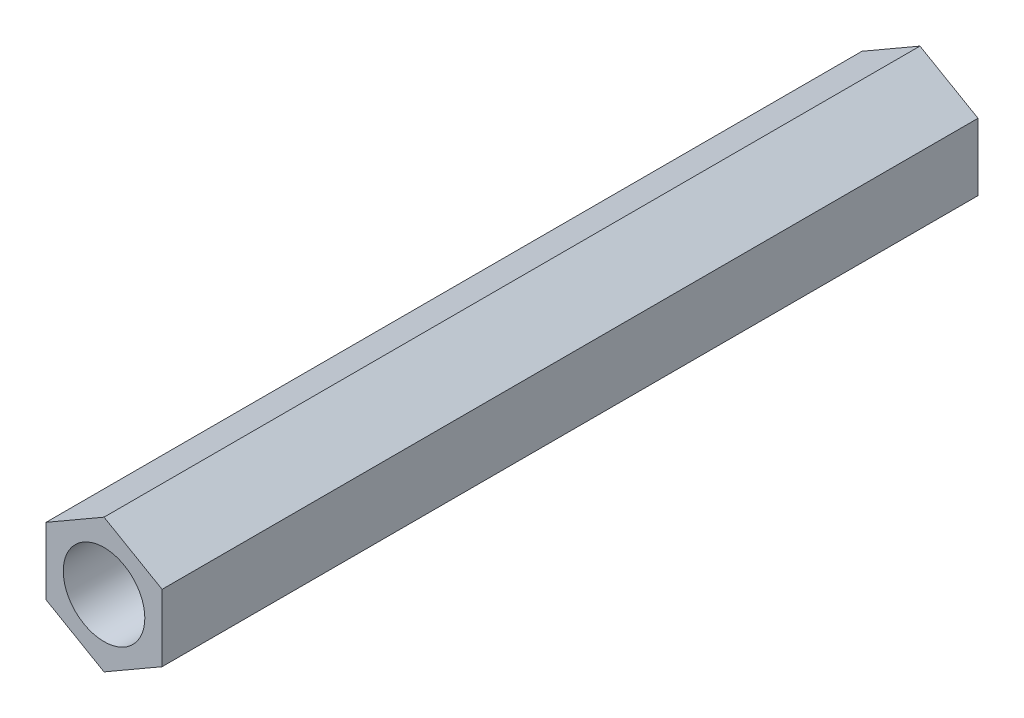
SolidWorks part; units mm, degrees
ref_plane "前视基准面" through (0, 0, 0) normal (0, 0, 1) x (1, 0, 0)
ref_plane "上视基准面" through (0, 0, 0) normal (0, 1, 0) x (1, 0, 0)
ref_plane "右视基准面" through (0, 0, 0) normal (1, 0, 0) x (0, 0, -1)
sketch "草图1" plane through (0, 0, 0) normal (0, 0, 1) x (1, 0, 0)
  line L1 (0, 2.4639) -> (-2.1338, 1.232)
  line L2 (-2.1338, 1.232) -> (-2.1338, -1.232)
  line L3 (-2.1338, -1.232) -> (0, -2.4639)
  line L4 (0, -2.4639) -> (2.1338, -1.232)
  line L5 (2.1338, -1.232) -> (2.1338, 1.232)
  line L6 (2.1338, 1.232) -> (0, 2.4639)
  circle A0 centre (0, 0) radius 1.5
  circle A1 centre (0, 0) radius 2.1338 construction
extrude "凸台-拉伸1" add sketch "草图1" along normal blind 30
